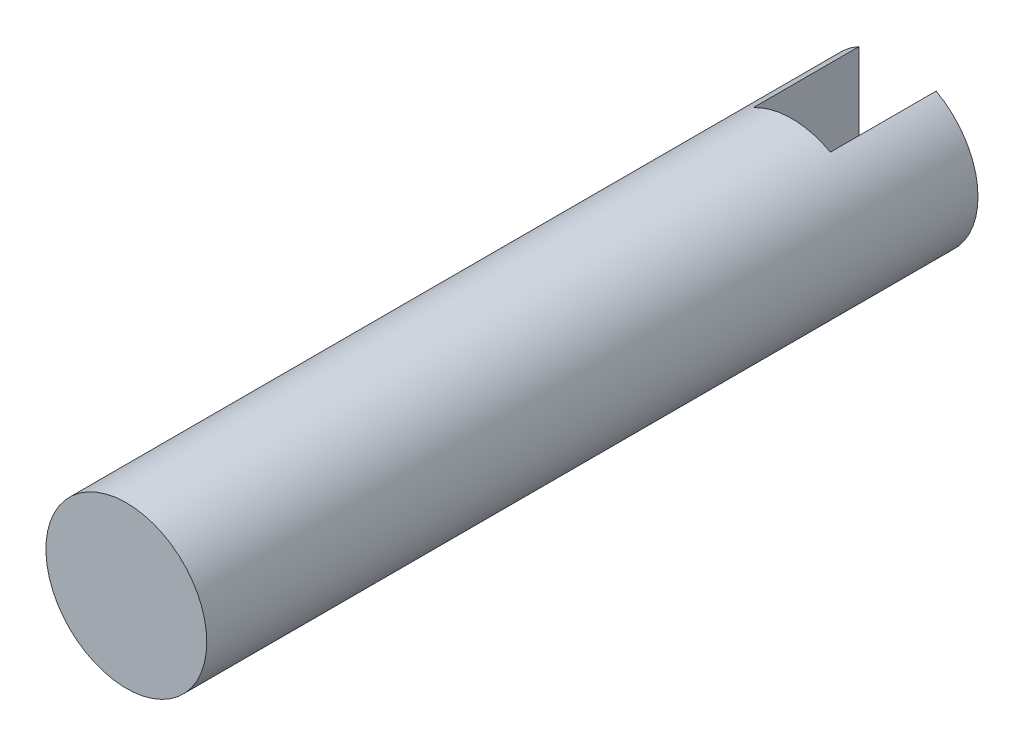
SolidWorks part; units mm, degrees
ref_plane "Plan de face" through (0, 0, 0) normal (0, 0, 1) x (1, 0, 0)
ref_plane "Plan de dessus" through (0, 0, 0) normal (0, 1, 0) x (1, 0, 0)
ref_plane "Plan de droite" through (0, 0, 0) normal (1, 0, 0) x (0, 0, -1)
sketch "Esquisse1" plane through (0, 0, 0) normal (0, 0, 1) x (1, 0, 0)
  circle A0 centre (0, 0) radius 3.65
  dimension "D1" = 7.3
extrude "Boss.-Extru.1" add sketch "Esquisse1" along normal blind 35
sketch "Esquisse2" plane through (0, 0, 0) normal (0, 0, -1) x (-1, 0, 0)
  line L0 (0, 4) -> (0, -4) construction
  line L1 (1.75, 4) -> (1.75, -4)
  line L2 (-1.75, 4) -> (-1.75, -4)
  arc A0 (1.75, 4) -> (-1.75, 4) centre (0, 4) ccw
  arc A1 (-1.75, -4) -> (1.75, -4) centre (0, -4) ccw
  point P2 (0, 0)
  dimension "D2" = 8
  dimension "D1" = 3.5
extrude "Enlèv. mat.-Extru.1" cut sketch "Esquisse2" against normal blind 4.8 contours A0 L2 A1 L1
